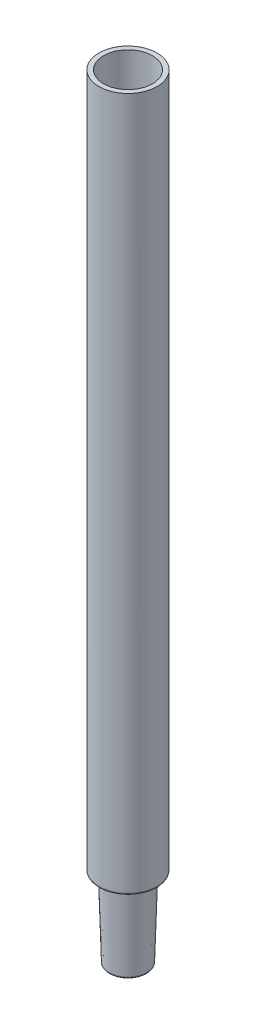
SolidWorks part; units mm, degrees
ref_plane "Ebene vorne" through (0, 0, 0) normal (0, 0, 1) x (1, 0, 0)
ref_plane "Ebene oben" through (0, 0, 0) normal (0, 1, 0) x (1, 0, 0)
ref_plane "Ebene rechts" through (0, 0, 0) normal (1, 0, 0) x (0, 0, -1)
sketch "Skizze1" plane through (0, 0, 0) normal (0, 0, 1) x (1, 0, 0)
  line L1 (-2.6, 82.5) -> (-3.1, 82.5)
  line L2 (-3.1, 82.5) -> (-3.1, 8.5)
  line L4 (0, 0) -> (0, -28.3945) construction
  line L14 (-2.6, 9) -> (-2.6, 82.5)
  line L15 (-2.6, 9) -> (-1.7647, 9)
  line L17 (-1.7647, 9) -> (-1.5, 0)
  line L18 (-1.5, 0) -> (-2, 0)
  line L19 (-2, 0) -> (-2.25, 8.5)
  line L21 (-2.25, 8.5) -> (-3.1, 8.5)
  dimension "D1" = 0.5
  dimension "D2" = 2.25
  dimension "D3" = 3.1
  dimension "D4" = 0.5
  dimension "D5" = 2
  dimension "D6" = 0.5
  dimension "D7" = 8.5
  dimension "D8" = 74
revolve "Rotation1" add sketch "Skizze1" angle 360 about L4
sketch "Skizze2" plane through (0, 82.5, 0) normal (0, 1, 0) x (1, 0, 0)
  circle A0 centre (0, 0) radius 3.1 construction
  circle A1 centre (0, 0) radius 2.6 construction
  circle A2 centre (0, 0) radius 2.6
  ellipse E0 centre (0, 0) end of major axis (10, 0) minor radius 3.1
  dimension "D1" = 20
extrude "Aufsatz-Linear austragen1" [suppressed] add sketch "Skizze2" against normal blind 1
fillet "Verrundung1" radius 0.2 4 edges at (-1.5, 0, 0) (-2, 0, 0) (-2.25, 8.5, 0) (-3.1, 8.5, 0)
